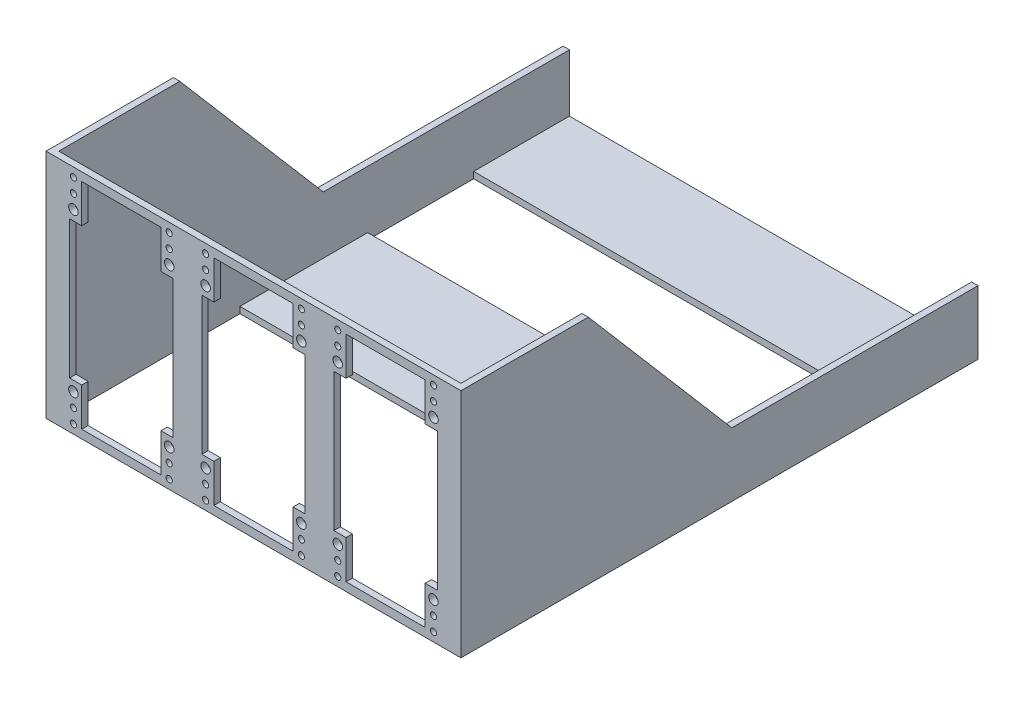
SolidWorks part; units mm, degrees
ref_plane "Front Plane" through (0, 0, 0) normal (0, 0, 1) x (1, 0, 0)
ref_plane "Top Plane" through (0, 0, 0) normal (0, 1, 0) x (1, 0, 0)
ref_plane "Right Plane" through (0, 0, 0) normal (1, 0, 0) x (0, 0, -1)
sketch "Sketch1" plane through (0, 0, 0) normal (0, 0, 1) x (1, 0, 0)
  line L8 (177.1103, 119.2472) -> (342.2103, 119.2472)
  line L9 (177.1103, 119.2472) -> (177.1103, 27.1722)
  line L10 (177.1103, 27.1722) -> (342.2103, 27.1722)
  line L11 (342.2103, 119.2472) -> (342.2103, 27.1722)
  dimension "D1" = 165.1
  dimension "D2" = 92.075
extrude "Boss-Extrude1" add sketch "Sketch1" against normal blind 2.54
sketch "Sketch2" plane through (0, 0, 0) normal (0, 0, 1) x (1, 0, 0)
  line L0 (227.6563, 73.2097) -> (239.0863, 73.2097) construction
  line L1 (280.2343, 73.2097) -> (291.6643, 73.2097) construction
  line L2 (186.5083, 73.2097) -> (177.1103, 73.2097) construction
  line L3 (177.1103, 119.2472) -> (177.1103, 27.1722) construction
  line L4 (332.8123, 64.776) -> (342.2103, 64.776) construction
  line L5 (342.2103, 119.2472) -> (342.2103, 27.1722) construction
  line L6 (212.904, 115.8817) -> (212.904, 119.2472) construction
  line L8 (177.1103, 119.2472) -> (342.2103, 119.2472) construction
  line L11 (207.0823, 30.5377) -> (207.0823, 27.1722) construction
  line L12 (177.1103, 27.1722) -> (342.2103, 27.1722) construction
  line B0 (191.3343, 115.8817) -> (222.8303, 115.8817)
  line B1 (191.3343, 115.8817) -> (191.3343, 100.6417)
  line B2 (191.3343, 100.6417) -> (186.5083, 100.6417)
  line B3 (186.5083, 100.6417) -> (186.5083, 45.7777)
  line B4 (186.5083, 45.7777) -> (191.3343, 45.7777)
  line B5 (191.3343, 45.7777) -> (191.3343, 30.5377)
  line B6 (191.3343, 30.5377) -> (222.8303, 30.5377)
  line B7 (222.8303, 30.5377) -> (222.8303, 45.7777)
  line B8 (222.8303, 45.7777) -> (227.6563, 45.7777)
  line B9 (227.6563, 45.7777) -> (227.6563, 100.6417)
  line B10 (227.6563, 100.6417) -> (222.8303, 100.6417)
  line B11 (222.8303, 100.6417) -> (222.8303, 115.8817)
  circle B12 centre (188.0323, 41.8153) radius 1.905
  circle B13 centre (226.1323, 104.6041) radius 1.905
  circle B14 centre (188.0323, 104.6041) radius 1.905
  circle B15 centre (188.0323, 36.2781) radius 1.2192
  circle B16 centre (188.0323, 30.7155) radius 1.2192
  circle B17 centre (226.1323, 41.8153) radius 1.905
  circle B18 centre (226.1323, 36.2781) radius 1.2192
  circle B19 centre (226.1323, 30.7155) radius 1.2192
  circle B20 centre (226.1323, 110.1413) radius 1.2192
  circle B21 centre (226.1323, 115.7039) radius 1.2192
  circle B22 centre (188.0323, 110.1413) radius 1.2192
  circle B23 centre (188.0323, 115.7039) radius 1.2192
  line B24 (243.9123, 115.8817) -> (275.4083, 115.8817)
  line B25 (243.9123, 115.8817) -> (243.9123, 100.6417)
  line B26 (243.9123, 100.6417) -> (239.0863, 100.6417)
  line B27 (239.0863, 100.6417) -> (239.0863, 45.7777)
  line B28 (239.0863, 45.7777) -> (243.9123, 45.7777)
  line B29 (243.9123, 45.7777) -> (243.9123, 30.5377)
  line B30 (243.9123, 30.5377) -> (275.4083, 30.5377)
  line B31 (275.4083, 30.5377) -> (275.4083, 45.7777)
  line B32 (275.4083, 45.7777) -> (280.2343, 45.7777)
  line B33 (280.2343, 45.7777) -> (280.2343, 100.6417)
  line B34 (280.2343, 100.6417) -> (275.4083, 100.6417)
  line B35 (275.4083, 100.6417) -> (275.4083, 115.8817)
  circle B36 centre (240.6103, 41.8153) radius 1.905
  circle B37 centre (278.7103, 104.6041) radius 1.905
  circle B38 centre (240.6103, 104.6041) radius 1.905
  circle B39 centre (240.6103, 36.2781) radius 1.2192
  circle B40 centre (240.6103, 30.7155) radius 1.2192
  circle B41 centre (278.7103, 41.8153) radius 1.905
  circle B42 centre (278.7103, 36.2781) radius 1.2192
  circle B43 centre (278.7103, 30.7155) radius 1.2192
  circle B44 centre (278.7103, 110.1413) radius 1.2192
  circle B45 centre (278.7103, 115.7039) radius 1.2192
  circle B46 centre (240.6103, 110.1413) radius 1.2192
  circle B47 centre (240.6103, 115.7039) radius 1.2192
  line B48 (296.4903, 115.8817) -> (327.9863, 115.8817)
  line B49 (296.4903, 115.8817) -> (296.4903, 100.6417)
  line B50 (296.4903, 100.6417) -> (291.6643, 100.6417)
  line B51 (291.6643, 100.6417) -> (291.6643, 45.7777)
  line B52 (291.6643, 45.7777) -> (296.4903, 45.7777)
  line B53 (296.4903, 45.7777) -> (296.4903, 30.5377)
  line B54 (296.4903, 30.5377) -> (327.9863, 30.5377)
  line B55 (327.9863, 30.5377) -> (327.9863, 45.7777)
  line B56 (327.9863, 45.7777) -> (332.8123, 45.7777)
  line B57 (332.8123, 45.7777) -> (332.8123, 100.6417)
  line B58 (332.8123, 100.6417) -> (327.9863, 100.6417)
  line B59 (327.9863, 100.6417) -> (327.9863, 115.8817)
  circle B60 centre (293.1883, 41.8153) radius 1.905
  circle B61 centre (331.2883, 104.6041) radius 1.905
  circle B62 centre (293.1883, 104.6041) radius 1.905
  circle B63 centre (293.1883, 36.2781) radius 1.2192
  circle B64 centre (293.1883, 30.7155) radius 1.2192
  circle B65 centre (331.2883, 41.8153) radius 1.905
  circle B66 centre (331.2883, 36.2781) radius 1.2192
  circle B67 centre (331.2883, 30.7155) radius 1.2192
  circle B68 centre (331.2883, 110.1413) radius 1.2192
  circle B69 centre (331.2883, 115.7039) radius 1.2192
  circle B70 centre (293.1883, 110.1413) radius 1.2192
  circle B71 centre (293.1883, 115.7039) radius 1.2192
sketch_block_instance "Button Panel-1"
sketch_block "Button Panel" parameters "D7"=2.4384, "D14"=3.81, "D1"=85.344, "D2"=31.496, "D3"=38.1, "D4"=62.7888, "D5"=5.5372, "D6"=5.5626, "D8"=5.5372, "D9"=5.5626, "D10"=5.5372, "D11"=5.5372, "D12"=4.826, "D13"=3.302, "D15"=5.5626
sketch_block_instance "Button Panel-3"
sketch_block_instance "Button Panel-4" parameters "D1"=7.5946, "D2"=196.9279
extrude "Cut-Extrude1" cut sketch "Sketch2" against normal blind 2.54
sketch "Sketch4" plane through (0, 0, -2.54) normal (0, 0, -1) x (-1, 0, 0)
  line L0 (-177.1103, 27.1722) -> (-342.2103, 27.1722) construction
  line L1 (-342.2103, 119.2472) -> (-339.6703, 119.2472)
  line L2 (-342.2103, 119.2472) -> (-342.2103, 27.1722)
  line L3 (-342.2103, 27.1722) -> (-339.6703, 27.1722)
  line L4 (-339.6703, 119.2472) -> (-339.6703, 27.1722)
  line L6 (-177.1103, 119.2472) -> (-179.6503, 119.2472)
  line L7 (-177.1103, 119.2472) -> (-177.1103, 27.1722)
  line L8 (-177.1103, 27.1722) -> (-179.6503, 27.1722)
  line L9 (-179.6503, 119.2472) -> (-179.6503, 27.1722)
  dimension "D1" = 2.54
extrude "Boss-Extrude3" add sketch "Sketch4" along normal blind 203.2
sketch "Sketch6" plane through (339.6703, 0, 0) normal (-1, 0, 0) x (0, 0, 1)
  line L1 (-205.74, 27.1722) -> (-167.64, 27.1722)
  line L2 (-205.74, 27.1722) -> (-205.74, 29.7122)
  line L3 (-205.74, 29.7122) -> (-167.64, 29.7122)
  line L4 (-167.64, 27.1722) -> (-167.64, 29.7122)
  dimension "D1" = 38.1
  dimension "D2" = 2.54
extrude "Boss-Extrude4" add sketch "Sketch6" along normal up to surface (160.02 mm away) up to face at (179.6503, 73.2097, -104.14)
sketch "Sketch7" plane through (0, 27.1722, 0) normal (0, -1, 0) x (1, 0, 0)
  line L0 (179.6503, -167.64) -> (179.6503, -2.54) construction
  line L1 (179.6503, -125.4373) -> (339.6703, -125.4373)
  line L2 (179.6503, -125.4373) -> (179.6503, -74.6373)
  line L3 (179.6503, -74.6373) -> (339.6703, -74.6373)
  line L4 (339.6703, -125.4373) -> (339.6703, -74.6373)
  line L5 (339.6703, -167.64) -> (339.6703, -2.54) construction
  dimension "D1" = 50.8
extrude "Boss-Extrude5" add sketch "Sketch7" against normal blind 2.54
sketch "Sketch8" plane through (342.2103, 0, 0) normal (1, 0, 0) x (0, 0, -1)
  line L0 (12.593, 119.2472) -> (50.693, 119.2472)
  line L1 (205.74, 119.2472) -> (0, 119.2472) construction
  line L2 (50.693, 119.2472) -> (107.7811, 52.5722)
  line L3 (107.7811, 52.5722) -> (205.74, 52.5722)
  line L4 (205.74, 119.2472) -> (205.74, 27.1722) construction
  line L5 (205.74, 52.5722) -> (205.74, 119.2472)
  line L6 (205.74, 119.2472) -> (50.693, 119.2472)
  line M3 (205.74, 27.1722) -> (205.74, 119.2472)
  line M4 (205.74, 119.2472) -> (0, 119.2472)
  dimension "D1" = 25.4
  dimension "D2" = 38.1
extrude "Cut-Extrude2" cut sketch "Sketch8" against normal through all and the other way through all contours L2 L3 M3 M4
